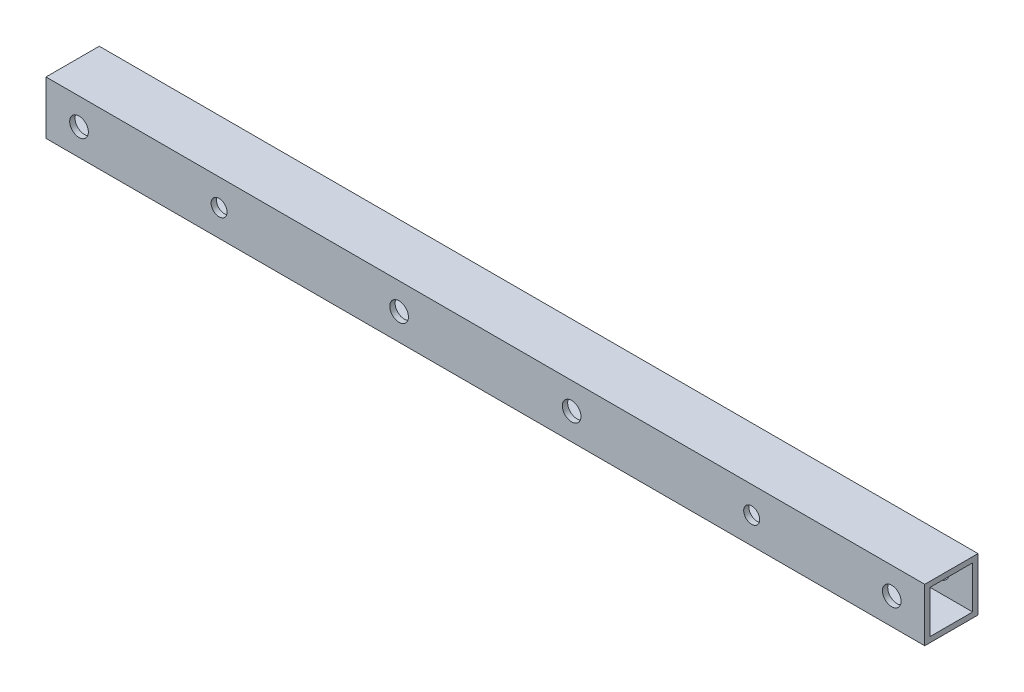
SolidWorks part; units mm, degrees
material "6063-O"
ref_plane "前视基准面" through (0, 0, 0) normal (0, 0, 1) x (1, 0, 0)
ref_plane "上视基准面" through (0, 0, 0) normal (0, 1, 0) x (1, 0, 0)
ref_plane "右视基准面" through (0, 0, 0) normal (1, 0, 0) x (0, 0, -1)
other "Configuration Table"
sketch "草图2" plane through (0, 0, 0) normal (1, 0, 0) x (0, 0, -1)
  line L1 (-5, -5) -> (5, -5)
  line L2 (-5, -5) -> (-5, 5)
  line L3 (-5, 5) -> (5, 5)
  line L4 (5, -5) -> (5, 5)
  line L5 (-5, -5) -> (5, 5) construction
  line L6 (-5, 5) -> (5, -5) construction
  point P0 (0, 0)
  dimension "D1" = 10
  dimension "D2" = 10
extrude "拉伸-薄壁1" add sketch "草图2" against normal blind 165 thin thin type one direction reverse wall 1
sketch "草图3" plane through (0, 0, 5) normal (0, 0, 1) x (1, 0, 0)
  line L0 (-82.5, -5) -> (-82.5, 5) construction
  line L1 (-165, -5) -> (0, -5) construction
  line L2 (-165, 5) -> (0, 5) construction
  line L4 (0, 0) -> (-6.2, 0) construction
  line L5 (0, 5) -> (0, -5) construction
  line L6 (-82.5, 0) -> (-6.2, 0) construction
  circle A0 centre (-82.5, 0) radius 1.5 construction
  circle A2 centre (-6.2, 0) radius 1.75
  circle A3 centre (-158.8, 0) radius 1.75
  circle A4 centre (-32.5, 0) radius 1.5
  circle A5 centre (-132.5, 0) radius 1.5
  circle A6 centre (-66.3, 0) radius 1.75
  circle A7 centre (-98.7, 0) radius 1.75
  circle A8 centre (-47.5, 0) radius 1.5 construction
  circle A9 centre (-117.5, 0) radius 1.5 construction
  dimension "D1" = 3
  dimension "D2" = 32.4
  dimension "D3" = 3.5
  dimension "D5" = 100
  dimension "D4" = 152.6
  dimension "D6" = 70
  dimension "D7" = 3.5
extrude "切除-拉伸1" cut sketch "草图3" against normal through all
